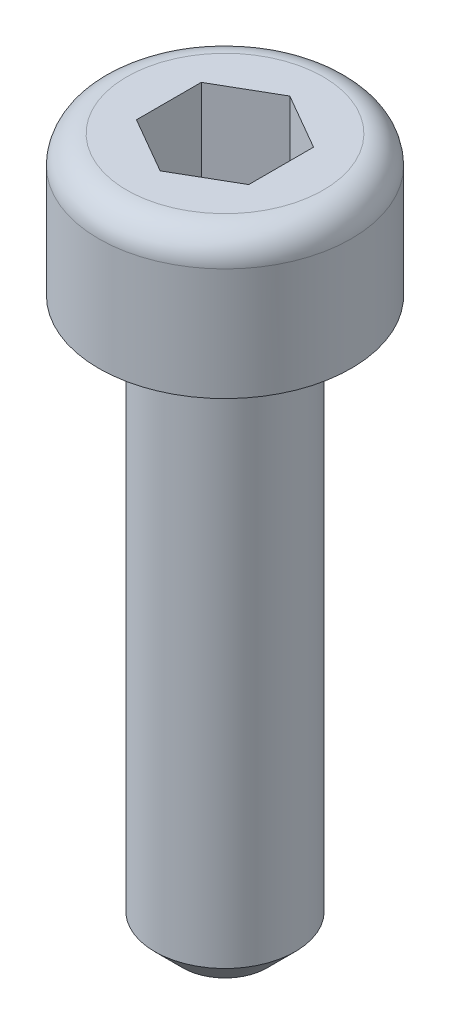
SolidWorks part; units mm, degrees
material "acero"
ref_plane "Alzado" through (0, 0, 0) normal (0, 0, 1) x (1, 0, 0)
ref_plane "Planta" through (0, 0, 0) normal (0, 1, 0) x (1, 0, 0)
ref_plane "Vista lateral" through (0, 0, 0) normal (1, 0, 0) x (0, 0, -1)
sketch "Croquis1" plane through (0, 0, 0) normal (0, 0, 1) x (1, 0, 0)
  line L0 (0, 0) -> (0, -60.9498) construction
  line L1 (0, 0) -> (2.25, 0)
  line L2 (2.25, 0) -> (2.25, -2.5)
  line L3 (2.25, -2.5) -> (1.25, -2.5)
  line L4 (1.25, -2.5) -> (1.25, -12.5)
  line L5 (1.25, -12.5) -> (0, -12.5)
  line L6 (0, -12.5) -> (0, 0)
  dimension "D1" = 10
  dimension "D2" = 2.5
  dimension "D3" = 4.5
  dimension "D4" = 2.5
revolve "Revolución1" add sketch "Croquis1" angle 360 about L0
sketch "Croquis2" plane through (0, 0, 0) normal (0, 1, 0) x (1, 0, 0)
  line L1 (1, 0.5774) -> (0, 1.1547)
  line L2 (0, 1.1547) -> (-1, 0.5774)
  line L3 (-1, 0.5774) -> (-1, -0.5774)
  line L4 (-1, -0.5774) -> (0, -1.1547)
  line L5 (0, -1.1547) -> (1, -0.5774)
  line L6 (1, -0.5774) -> (1, 0.5774)
  circle A0 centre (0, 0) radius 1 construction
  dimension "D1" = 2
extrude "Cortar-Extruir1" cut sketch "Croquis2" against normal blind 2
chamfer "Chaflán1" distance 0.5 angle 45 1 edges at (0, -12.5, 1.25)
fillet "Redondeo1" radius 0.5 1 edges at (0, 0, 2.25)
